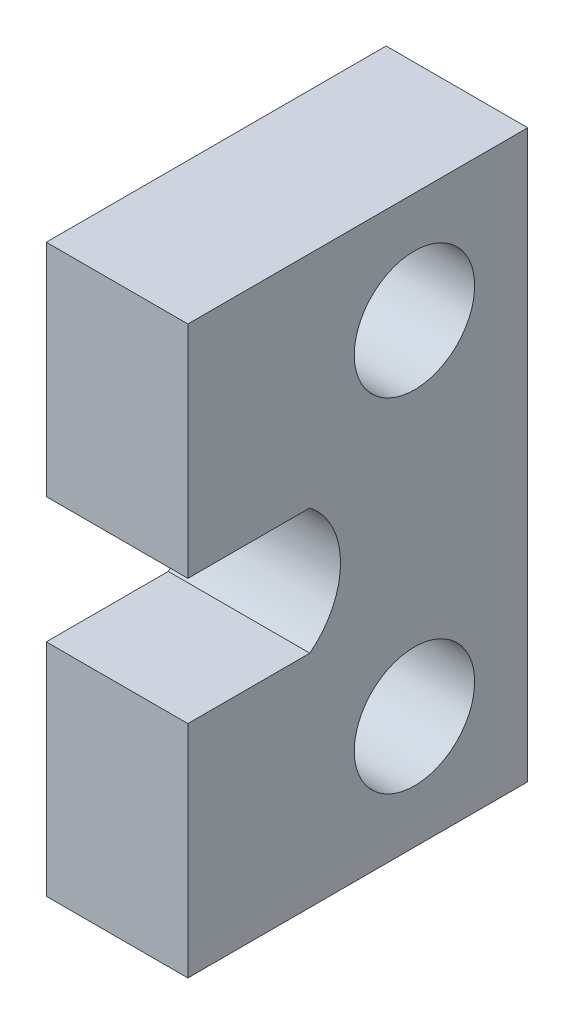
SolidWorks part; units mm, degrees
material "Plain Carbon Steel"
ref_plane "Front Plane" through (0, 0, 0) normal (0, 0, 1) x (1, 0, 0)
ref_plane "Top Plane" through (0, 0, 0) normal (0, 1, 0) x (1, 0, 0)
ref_plane "Right Plane" through (0, 0, 0) normal (1, 0, 0) x (0, 0, -1)
sketch "Sketch1" plane through (0, 0, 0) normal (0, 0, 1) x (1, 0, 0)
  line L1 (0, 0) -> (15.875, 0)
  line L2 (0, 0) -> (0, 63.5)
  line L3 (0, 63.5) -> (15.875, 63.5)
  line L4 (15.875, 0) -> (15.875, 63.5)
  dimension "D1" = 63.5
  dimension "D2" = 15.875
extrude "Boss-Extrude1" add sketch "Sketch1" along normal blind 38.1
sketch "Sketch2" plane through (0, 0, 0) normal (-1, 0, 0) x (0, 0, 1)
  line L0 (0, 31.75) -> (31.75, 31.75)
  line L1 (37.2412, 38.7985) -> (24.428, 38.7985)
  line L2 (24.428, 24.7015) -> (37.2412, 24.7015)
  line L3 (30.8346, 38.7985) -> (30.8346, 24.7015)
  line L4 (24.428, 38.7985) -> (0, 38.7985)
  line L5 (24.428, 24.7015) -> (0, 24.7015)
  line L6 (0, 63.5) -> (0, 0) construction
  line L7 (38.1, 63.5) -> (38.1, 0) construction
  line L8 (37.2412, 38.7985) -> (38.1, 38.7985)
  line L9 (37.2412, 38.7985) -> (37.2412, 24.7015)
  line L10 (37.2412, 24.7015) -> (38.1, 24.7015)
  line L11 (38.1, 38.7985) -> (38.1, 24.7015)
  arc A0 (37.2412, 38.7985) -> (37.2412, 24.7015) centre (31.75, 31.75) cw
  arc A1 (24.428, 38.7985) -> (24.428, 24.7015) centre (29.9192, 31.75) ccw
  point P10 (40.685, 31.75)
  point P17 (0, 31.75)
  dimension "D1" = 31.75
  dimension "D2" = 12.8132
  dimension "D3" = 12.8132
  dimension "D4" = 14.097
  dimension "D5" = 8.935
extrude "Cut-Extrude1" cut sketch "Sketch2" against normal through all
sketch "Sketch3" plane through (0, 0, 0) normal (-1, 0, 0) x (0, 0, 1)
  line L0 (12.7, 0) -> (12.7, 12.7)
  line L2 (12.7, 63.8492) -> (12.7, 51.1493)
  line L4 (0, 51.1493) -> (12.7, 51.1493)
  line L5 (0, 63.5) -> (0, 0) construction
  circle A0 centre (12.7, 51.1493) radius 6.7469
  circle A1 centre (12.7, 12.7) radius 6.7469
  dimension "D3" = 13.4937
  dimension "D4" = 13.4937
  dimension "D1" = 12.7
  dimension "D2" = 12.7
  dimension "D5" = 12.7
extrude "Cut-Extrude2" cut sketch "Sketch3" against normal through all
equation "\"D2@Sketch3\"=\"D1@Sketch3\""
equation "\"D4@Sketch3\"=\"D3@Sketch3\""
equation "\"D5@Sketch3\"=\"D1@Sketch3\""
